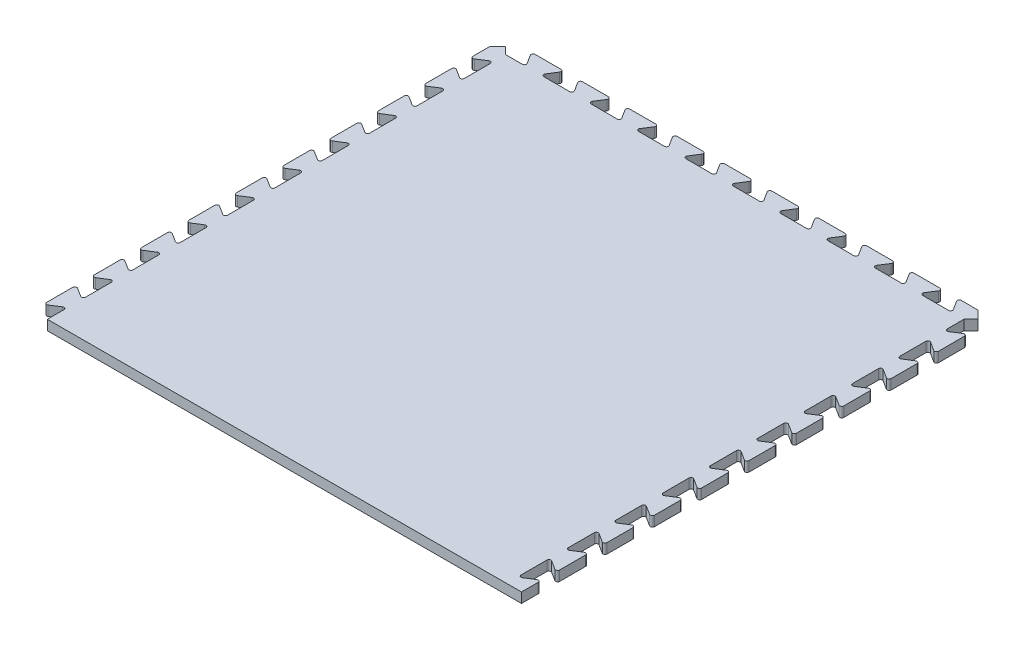
SolidWorks part; units mm, degrees
ref_plane "Front Plane" through (0, 0, 0) normal (0, 0, 1) x (1, 0, 0)
ref_plane "Top Plane" through (0, 0, 0) normal (0, 1, 0) x (1, 0, 0)
ref_plane "Right Plane" through (0, 0, 0) normal (1, 0, 0) x (0, 0, -1)
ref_plane "Plane1" through (0, 0, 0) normal (0, -1, 0) x (1, 0, 0)
sketch "Sketch1" plane through (0, 0, 0) normal (0, -1, 0) x (1, 0, 0)
  line L0 (310.9414, 290.7358) -> (-291.8914, 291.8914)
  line L1 (-291.8914, 291.8914) -> (-291.8914, 270.6042)
  line L2 (-295.7935, 268.4603) -> (-307.0392, 275.6056)
  line L3 (-310.9414, 273.4617) -> (-310.9414, 240.4417)
  line L4 (-307.0392, 238.2978) -> (-295.7935, 245.4431)
  line L5 (-291.8914, 243.2992) -> (-291.8914, 210.2792)
  line L6 (-295.7935, 208.1353) -> (-307.0392, 215.2806)
  line L7 (-310.9414, 213.1367) -> (-310.9414, 180.1167)
  line L8 (-307.0392, 177.9728) -> (-295.7935, 185.1181)
  line L9 (-291.8914, 182.9742) -> (-291.8914, 149.9542)
  line L10 (-295.7935, 147.8103) -> (-307.0392, 154.9556)
  line L11 (-310.9414, 152.8117) -> (-310.9414, 119.7917)
  line L12 (-307.0392, 117.6478) -> (-295.7935, 124.7931)
  line L13 (-291.8914, 122.6492) -> (-291.8914, 89.6292)
  line L14 (-295.7935, 87.4853) -> (-307.0392, 94.6306)
  line L15 (-310.9414, 92.4867) -> (-310.9414, 59.4667)
  line L16 (-307.0392, 57.3228) -> (-295.7935, 64.4681)
  line L17 (-291.8914, 62.3242) -> (-291.8914, 29.3042)
  line L18 (-295.7935, 27.1603) -> (-307.0392, 34.3056)
  line L19 (-310.9414, 32.1617) -> (-310.9414, -0.8583)
  line L20 (-307.0392, -3.0022) -> (-295.7935, 4.1431)
  line L21 (-291.8914, 1.9992) -> (-291.8914, -31.0208)
  line L22 (-295.7935, -33.1647) -> (-307.0392, -26.0194)
  line L23 (-310.9414, -28.1633) -> (-310.9414, -61.1833)
  line L24 (-307.0392, -63.3272) -> (-295.7935, -56.1819)
  line L25 (-291.8914, -58.3258) -> (-291.8914, -91.3458)
  line L26 (-295.7935, -93.4897) -> (-307.0392, -86.3444)
  line L27 (-310.9414, -88.4883) -> (-310.9414, -121.5083)
  line L28 (-307.0392, -123.6522) -> (-295.7935, -116.5069)
  line L29 (-291.8914, -118.6508) -> (-291.8914, -151.6708)
  line L30 (-295.7935, -153.8147) -> (-307.0392, -146.6694)
  line L31 (-310.9414, -148.8133) -> (-310.9414, -181.8333)
  line L32 (-307.0392, -183.9772) -> (-295.7935, -176.8319)
  line L33 (-291.8914, -178.9758) -> (-291.8914, -211.9958)
  line L34 (-295.7935, -214.1397) -> (-307.0392, -206.9944)
  line L35 (-310.9414, -209.1383) -> (-310.9414, -242.1583)
  line L36 (-307.0392, -244.3022) -> (-295.7935, -237.1569)
  line L37 (-291.8914, -239.3008) -> (-291.8914, -272.3208)
  line L38 (-295.7935, -274.4647) -> (-307.0392, -267.3194)
  line L39 (-310.9414, -269.4633) -> (-310.9414, -290.7358)
  line L40 (-310.9414, -290.7358) -> (-300.8386, -300.8386)
  line L41 (-300.8386, -300.8386) -> (-291.8914, -291.8914)
  line L42 (-291.8914, -291.8914) -> (-270.6042, -291.8914)
  line L43 (-268.4603, -295.7935) -> (-275.6056, -307.0392)
  line L44 (-273.4617, -310.9414) -> (-240.4417, -310.9414)
  line L45 (-238.2978, -307.0392) -> (-245.4431, -295.7935)
  line L46 (-243.2992, -291.8914) -> (-210.2792, -291.8914)
  line L47 (-208.1353, -295.7935) -> (-215.2806, -307.0392)
  line L48 (-213.1367, -310.9414) -> (-180.1167, -310.9414)
  line L49 (-177.9728, -307.0392) -> (-185.1181, -295.7935)
  line L50 (-182.9742, -291.8914) -> (-149.9542, -291.8914)
  line L51 (-147.8103, -295.7935) -> (-154.9556, -307.0392)
  line L52 (-152.8117, -310.9414) -> (-119.7917, -310.9414)
  line L53 (-117.6478, -307.0392) -> (-124.7931, -295.7935)
  line L54 (-122.6492, -291.8914) -> (-89.6292, -291.8914)
  line L55 (-87.4853, -295.7935) -> (-94.6306, -307.0392)
  line L56 (-92.4867, -310.9414) -> (-59.4667, -310.9414)
  line L57 (-57.3228, -307.0392) -> (-64.4681, -295.7935)
  line L58 (-62.3242, -291.8914) -> (-29.3042, -291.8914)
  line L59 (-27.1603, -295.7935) -> (-34.3056, -307.0392)
  line L60 (-32.1617, -310.9414) -> (0.8583, -310.9414)
  line L61 (3.0022, -307.0392) -> (-4.1431, -295.7935)
  line L62 (-1.9992, -291.8914) -> (31.0208, -291.8914)
  line L63 (33.1647, -295.7935) -> (26.0194, -307.0392)
  line L64 (28.1633, -310.9414) -> (61.1833, -310.9414)
  line L65 (63.3272, -307.0392) -> (56.1819, -295.7935)
  line L66 (58.3258, -291.8914) -> (91.3458, -291.8914)
  line L67 (93.4897, -295.7935) -> (86.3444, -307.0392)
  line L68 (88.4883, -310.9414) -> (121.5083, -310.9414)
  line L69 (123.6522, -307.0392) -> (116.5069, -295.7935)
  line L70 (118.6508, -291.8914) -> (151.6708, -291.8914)
  line L71 (153.8147, -295.7935) -> (146.6694, -307.0392)
  line L72 (148.8133, -310.9414) -> (181.8333, -310.9414)
  line L73 (183.9772, -307.0392) -> (176.8319, -295.7935)
  line L74 (178.9758, -291.8914) -> (211.9958, -291.8914)
  line L75 (214.1397, -295.7935) -> (206.9944, -307.0392)
  line L76 (209.1383, -310.9414) -> (242.1583, -310.9414)
  line L77 (244.3022, -307.0392) -> (237.1569, -295.7935)
  line L78 (239.3008, -291.8914) -> (272.3208, -291.8914)
  line L79 (274.4647, -295.7935) -> (267.3194, -307.0392)
  line L80 (269.4633, -310.9414) -> (290.7358, -310.9414)
  line L81 (290.7358, -310.9414) -> (300.8386, -300.8386)
  line L82 (300.8386, -300.8386) -> (291.8914, -291.8914)
  line L83 (291.8914, -291.8914) -> (291.8914, -270.6042)
  line L84 (295.7935, -268.4603) -> (307.0392, -275.6056)
  line L85 (310.9414, -273.4617) -> (310.9414, -240.4417)
  line L86 (307.0392, -238.2978) -> (295.7935, -245.4431)
  line L87 (291.8914, -243.2992) -> (291.8914, -210.2792)
  line L88 (295.7935, -208.1353) -> (307.0392, -215.2806)
  line L89 (310.9414, -213.1367) -> (310.9414, -180.1167)
  line L90 (307.0392, -177.9728) -> (295.7935, -185.1181)
  line L91 (291.8914, -182.9742) -> (291.8914, -149.9542)
  line L92 (295.7935, -147.8103) -> (307.0392, -154.9556)
  line L93 (310.9414, -152.8117) -> (310.9414, -119.7917)
  line L94 (307.0392, -117.6478) -> (295.7935, -124.7931)
  line L95 (291.8914, -122.6492) -> (291.8914, -89.6292)
  line L96 (295.7935, -87.4853) -> (307.0392, -94.6306)
  line L97 (310.9414, -92.4867) -> (310.9414, -59.4667)
  line L98 (307.0392, -57.3228) -> (295.7935, -64.4681)
  line L99 (291.8914, -62.3242) -> (291.8914, -29.3042)
  line L100 (295.7935, -27.1603) -> (307.0392, -34.3056)
  line L101 (310.9414, -32.1617) -> (310.9414, 0.8583)
  line L102 (307.0392, 3.0022) -> (295.7935, -4.1431)
  line L103 (291.8914, -1.9992) -> (291.8914, 31.0208)
  line L104 (295.7935, 33.1647) -> (307.0392, 26.0194)
  line L105 (310.9414, 28.1633) -> (310.9414, 61.1833)
  line L106 (307.0392, 63.3272) -> (295.7935, 56.1819)
  line L107 (291.8914, 58.3258) -> (291.8914, 91.3458)
  line L108 (295.7935, 93.4897) -> (307.0392, 86.3444)
  line L109 (310.9414, 88.4883) -> (310.9414, 121.5083)
  line L110 (307.0392, 123.6522) -> (295.7935, 116.5069)
  line L111 (291.8914, 118.6508) -> (291.8914, 151.6708)
  line L112 (295.7935, 153.8147) -> (307.0392, 146.6694)
  line L113 (310.9414, 148.8133) -> (310.9414, 181.8333)
  line L114 (307.0392, 183.9772) -> (295.7935, 176.8319)
  line L115 (291.8914, 178.9758) -> (291.8914, 211.9958)
  line L116 (295.7935, 214.1397) -> (307.0392, 206.9944)
  line L117 (310.9414, 209.1383) -> (310.9414, 242.1583)
  line L118 (307.0392, 244.3022) -> (295.7935, 237.1569)
  line L119 (291.8914, 239.3008) -> (291.8914, 272.3208)
  line L120 (295.7935, 274.4647) -> (307.0392, 267.3194)
  line L121 (310.9414, 269.4633) -> (310.9414, 290.7358)
  arc A0 (-291.8914, 270.6042) -> (-295.7935, 268.4603) centre (-294.4314, 270.6042) cw
  arc A1 (-307.0392, 275.6056) -> (-310.9414, 273.4617) centre (-308.4014, 273.4617) ccw
  arc A2 (-310.9414, 240.4417) -> (-307.0392, 238.2978) centre (-308.4014, 240.4417) ccw
  arc A3 (-295.7935, 245.4431) -> (-291.8914, 243.2992) centre (-294.4314, 243.2992) cw
  arc A4 (-291.8914, 210.2792) -> (-295.7935, 208.1353) centre (-294.4314, 210.2792) cw
  arc A5 (-307.0392, 215.2806) -> (-310.9414, 213.1367) centre (-308.4014, 213.1367) ccw
  arc A6 (-310.9414, 180.1167) -> (-307.0392, 177.9728) centre (-308.4014, 180.1167) ccw
  arc A7 (-295.7935, 185.1181) -> (-291.8914, 182.9742) centre (-294.4314, 182.9742) cw
  arc A8 (-291.8914, 149.9542) -> (-295.7935, 147.8103) centre (-294.4314, 149.9542) cw
  arc A9 (-307.0392, 154.9556) -> (-310.9414, 152.8117) centre (-308.4014, 152.8117) ccw
  arc A10 (-310.9414, 119.7917) -> (-307.0392, 117.6478) centre (-308.4014, 119.7917) ccw
  arc A11 (-295.7935, 124.7931) -> (-291.8914, 122.6492) centre (-294.4314, 122.6492) cw
  arc A12 (-291.8914, 89.6292) -> (-295.7935, 87.4853) centre (-294.4314, 89.6292) cw
  arc A13 (-307.0392, 94.6306) -> (-310.9414, 92.4867) centre (-308.4014, 92.4867) ccw
  arc A14 (-310.9414, 59.4667) -> (-307.0392, 57.3228) centre (-308.4014, 59.4667) ccw
  arc A15 (-295.7935, 64.4681) -> (-291.8914, 62.3242) centre (-294.4314, 62.3242) cw
  arc A16 (-291.8914, 29.3042) -> (-295.7935, 27.1603) centre (-294.4314, 29.3042) cw
  arc A17 (-307.0392, 34.3056) -> (-310.9414, 32.1617) centre (-308.4014, 32.1617) ccw
  arc A18 (-310.9414, -0.8583) -> (-307.0392, -3.0022) centre (-308.4014, -0.8583) ccw
  arc A19 (-295.7935, 4.1431) -> (-291.8914, 1.9992) centre (-294.4314, 1.9992) cw
  arc A20 (-291.8914, -31.0208) -> (-295.7935, -33.1647) centre (-294.4314, -31.0208) cw
  arc A21 (-307.0392, -26.0194) -> (-310.9414, -28.1633) centre (-308.4014, -28.1633) ccw
  arc A22 (-310.9414, -61.1833) -> (-307.0392, -63.3272) centre (-308.4014, -61.1833) ccw
  arc A23 (-295.7935, -56.1819) -> (-291.8914, -58.3258) centre (-294.4314, -58.3258) cw
  arc A24 (-291.8914, -91.3458) -> (-295.7935, -93.4897) centre (-294.4314, -91.3458) cw
  arc A25 (-307.0392, -86.3444) -> (-310.9414, -88.4883) centre (-308.4014, -88.4883) ccw
  arc A26 (-310.9414, -121.5083) -> (-307.0392, -123.6522) centre (-308.4014, -121.5083) ccw
  arc A27 (-295.7935, -116.5069) -> (-291.8914, -118.6508) centre (-294.4314, -118.6508) cw
  arc A28 (-291.8914, -151.6708) -> (-295.7935, -153.8147) centre (-294.4314, -151.6708) cw
  arc A29 (-307.0392, -146.6694) -> (-310.9414, -148.8133) centre (-308.4014, -148.8133) ccw
  arc A30 (-310.9414, -181.8333) -> (-307.0392, -183.9772) centre (-308.4014, -181.8333) ccw
  arc A31 (-295.7935, -176.8319) -> (-291.8914, -178.9758) centre (-294.4314, -178.9758) cw
  arc A32 (-291.8914, -211.9958) -> (-295.7935, -214.1397) centre (-294.4314, -211.9958) cw
  arc A33 (-307.0392, -206.9944) -> (-310.9414, -209.1383) centre (-308.4014, -209.1383) ccw
  arc A34 (-310.9414, -242.1583) -> (-307.0392, -244.3022) centre (-308.4014, -242.1583) ccw
  arc A35 (-295.7935, -237.1569) -> (-291.8914, -239.3008) centre (-294.4314, -239.3008) cw
  arc A36 (-291.8914, -272.3208) -> (-295.7935, -274.4647) centre (-294.4314, -272.3208) cw
  arc A37 (-307.0392, -267.3194) -> (-310.9414, -269.4633) centre (-308.4014, -269.4633) ccw
  arc A38 (-270.6042, -291.8914) -> (-268.4603, -295.7935) centre (-270.6042, -294.4314) cw
  arc A39 (-275.6056, -307.0392) -> (-273.4617, -310.9414) centre (-273.4617, -308.4014) ccw
  arc A40 (-240.4417, -310.9414) -> (-238.2978, -307.0392) centre (-240.4417, -308.4014) ccw
  arc A41 (-245.4431, -295.7935) -> (-243.2992, -291.8914) centre (-243.2992, -294.4314) cw
  arc A42 (-210.2792, -291.8914) -> (-208.1353, -295.7935) centre (-210.2792, -294.4314) cw
  arc A43 (-215.2806, -307.0392) -> (-213.1367, -310.9414) centre (-213.1367, -308.4014) ccw
  arc A44 (-180.1167, -310.9414) -> (-177.9728, -307.0392) centre (-180.1167, -308.4014) ccw
  arc A45 (-185.1181, -295.7935) -> (-182.9742, -291.8914) centre (-182.9742, -294.4314) cw
  arc A46 (-149.9542, -291.8914) -> (-147.8103, -295.7935) centre (-149.9542, -294.4314) cw
  arc A47 (-154.9556, -307.0392) -> (-152.8117, -310.9414) centre (-152.8117, -308.4014) ccw
  arc A48 (-119.7917, -310.9414) -> (-117.6478, -307.0392) centre (-119.7917, -308.4014) ccw
  arc A49 (-124.7931, -295.7935) -> (-122.6492, -291.8914) centre (-122.6492, -294.4314) cw
  arc A50 (-89.6292, -291.8914) -> (-87.4853, -295.7935) centre (-89.6292, -294.4314) cw
  arc A51 (-94.6306, -307.0392) -> (-92.4867, -310.9414) centre (-92.4867, -308.4014) ccw
  arc A52 (-59.4667, -310.9414) -> (-57.3228, -307.0392) centre (-59.4667, -308.4014) ccw
  arc A53 (-64.4681, -295.7935) -> (-62.3242, -291.8914) centre (-62.3242, -294.4314) cw
  arc A54 (-29.3042, -291.8914) -> (-27.1603, -295.7935) centre (-29.3042, -294.4314) cw
  arc A55 (-34.3056, -307.0392) -> (-32.1617, -310.9414) centre (-32.1617, -308.4014) ccw
  arc A56 (0.8583, -310.9414) -> (3.0022, -307.0392) centre (0.8583, -308.4014) ccw
  arc A57 (-4.1431, -295.7935) -> (-1.9992, -291.8914) centre (-1.9992, -294.4314) cw
  arc A58 (31.0208, -291.8914) -> (33.1647, -295.7935) centre (31.0208, -294.4314) cw
  arc A59 (26.0194, -307.0392) -> (28.1633, -310.9414) centre (28.1633, -308.4014) ccw
  arc A60 (61.1833, -310.9414) -> (63.3272, -307.0392) centre (61.1833, -308.4014) ccw
  arc A61 (56.1819, -295.7935) -> (58.3258, -291.8914) centre (58.3258, -294.4314) cw
  arc A62 (91.3458, -291.8914) -> (93.4897, -295.7935) centre (91.3458, -294.4314) cw
  arc A63 (86.3444, -307.0392) -> (88.4883, -310.9414) centre (88.4883, -308.4014) ccw
  arc A64 (121.5083, -310.9414) -> (123.6522, -307.0392) centre (121.5083, -308.4014) ccw
  arc A65 (116.5069, -295.7935) -> (118.6508, -291.8914) centre (118.6508, -294.4314) cw
  arc A66 (151.6708, -291.8914) -> (153.8147, -295.7935) centre (151.6708, -294.4314) cw
  arc A67 (146.6694, -307.0392) -> (148.8133, -310.9414) centre (148.8133, -308.4014) ccw
  arc A68 (181.8333, -310.9414) -> (183.9772, -307.0392) centre (181.8333, -308.4014) ccw
  arc A69 (176.8319, -295.7935) -> (178.9758, -291.8914) centre (178.9758, -294.4314) cw
  arc A70 (211.9958, -291.8914) -> (214.1397, -295.7935) centre (211.9958, -294.4314) cw
  arc A71 (206.9944, -307.0392) -> (209.1383, -310.9414) centre (209.1383, -308.4014) ccw
  arc A72 (242.1583, -310.9414) -> (244.3022, -307.0392) centre (242.1583, -308.4014) ccw
  arc A73 (237.1569, -295.7935) -> (239.3008, -291.8914) centre (239.3008, -294.4314) cw
  arc A74 (272.3208, -291.8914) -> (274.4647, -295.7935) centre (272.3208, -294.4314) cw
  arc A75 (267.3194, -307.0392) -> (269.4633, -310.9414) centre (269.4633, -308.4014) ccw
  arc A76 (291.8914, -270.6042) -> (295.7935, -268.4603) centre (294.4314, -270.6042) cw
  arc A77 (307.0392, -275.6056) -> (310.9414, -273.4617) centre (308.4014, -273.4617) ccw
  arc A78 (310.9414, -240.4417) -> (307.0392, -238.2978) centre (308.4014, -240.4417) ccw
  arc A79 (295.7935, -245.4431) -> (291.8914, -243.2992) centre (294.4314, -243.2992) cw
  arc A80 (291.8914, -210.2792) -> (295.7935, -208.1353) centre (294.4314, -210.2792) cw
  arc A81 (307.0392, -215.2806) -> (310.9414, -213.1367) centre (308.4014, -213.1367) ccw
  arc A82 (310.9414, -180.1167) -> (307.0392, -177.9728) centre (308.4014, -180.1167) ccw
  arc A83 (295.7935, -185.1181) -> (291.8914, -182.9742) centre (294.4314, -182.9742) cw
  arc A84 (291.8914, -149.9542) -> (295.7935, -147.8103) centre (294.4314, -149.9542) cw
  arc A85 (307.0392, -154.9556) -> (310.9414, -152.8117) centre (308.4014, -152.8117) ccw
  arc A86 (310.9414, -119.7917) -> (307.0392, -117.6478) centre (308.4014, -119.7917) ccw
  arc A87 (295.7935, -124.7931) -> (291.8914, -122.6492) centre (294.4314, -122.6492) cw
  arc A88 (291.8914, -89.6292) -> (295.7935, -87.4853) centre (294.4314, -89.6292) cw
  arc A89 (307.0392, -94.6306) -> (310.9414, -92.4867) centre (308.4014, -92.4867) ccw
  arc A90 (310.9414, -59.4667) -> (307.0392, -57.3228) centre (308.4014, -59.4667) ccw
  arc A91 (295.7935, -64.4681) -> (291.8914, -62.3242) centre (294.4314, -62.3242) cw
  arc A92 (291.8914, -29.3042) -> (295.7935, -27.1603) centre (294.4314, -29.3042) cw
  arc A93 (307.0392, -34.3056) -> (310.9414, -32.1617) centre (308.4014, -32.1617) ccw
  arc A94 (310.9414, 0.8583) -> (307.0392, 3.0022) centre (308.4014, 0.8583) ccw
  arc A95 (295.7935, -4.1431) -> (291.8914, -1.9992) centre (294.4314, -1.9992) cw
  arc A96 (291.8914, 31.0208) -> (295.7935, 33.1647) centre (294.4314, 31.0208) cw
  arc A97 (307.0392, 26.0194) -> (310.9414, 28.1633) centre (308.4014, 28.1633) ccw
  arc A98 (310.9414, 61.1833) -> (307.0392, 63.3272) centre (308.4014, 61.1833) ccw
  arc A99 (295.7935, 56.1819) -> (291.8914, 58.3258) centre (294.4314, 58.3258) cw
  arc A100 (291.8914, 91.3458) -> (295.7935, 93.4897) centre (294.4314, 91.3458) cw
  arc A101 (307.0392, 86.3444) -> (310.9414, 88.4883) centre (308.4014, 88.4883) ccw
  arc A102 (310.9414, 121.5083) -> (307.0392, 123.6522) centre (308.4014, 121.5083) ccw
  arc A103 (295.7935, 116.5069) -> (291.8914, 118.6508) centre (294.4314, 118.6508) cw
  arc A104 (291.8914, 151.6708) -> (295.7935, 153.8147) centre (294.4314, 151.6708) cw
  arc A105 (307.0392, 146.6694) -> (310.9414, 148.8133) centre (308.4014, 148.8133) ccw
  arc A106 (310.9414, 181.8333) -> (307.0392, 183.9772) centre (308.4014, 181.8333) ccw
  arc A107 (295.7935, 176.8319) -> (291.8914, 178.9758) centre (294.4314, 178.9758) cw
  arc A108 (291.8914, 211.9958) -> (295.7935, 214.1397) centre (294.4314, 211.9958) cw
  arc A109 (307.0392, 206.9944) -> (310.9414, 209.1383) centre (308.4014, 209.1383) ccw
  arc A110 (310.9414, 242.1583) -> (307.0392, 244.3022) centre (308.4014, 242.1583) ccw
  arc A111 (295.7935, 237.1569) -> (291.8914, 239.3008) centre (294.4314, 239.3008) cw
  arc A112 (291.8914, 272.3208) -> (295.7935, 274.4647) centre (294.4314, 272.3208) cw
  arc A113 (307.0392, 267.3194) -> (310.9414, 269.4633) centre (308.4014, 269.4633) ccw
extrude "Boss-Extrude1" add sketch "Sketch1" against normal blind 12.7
